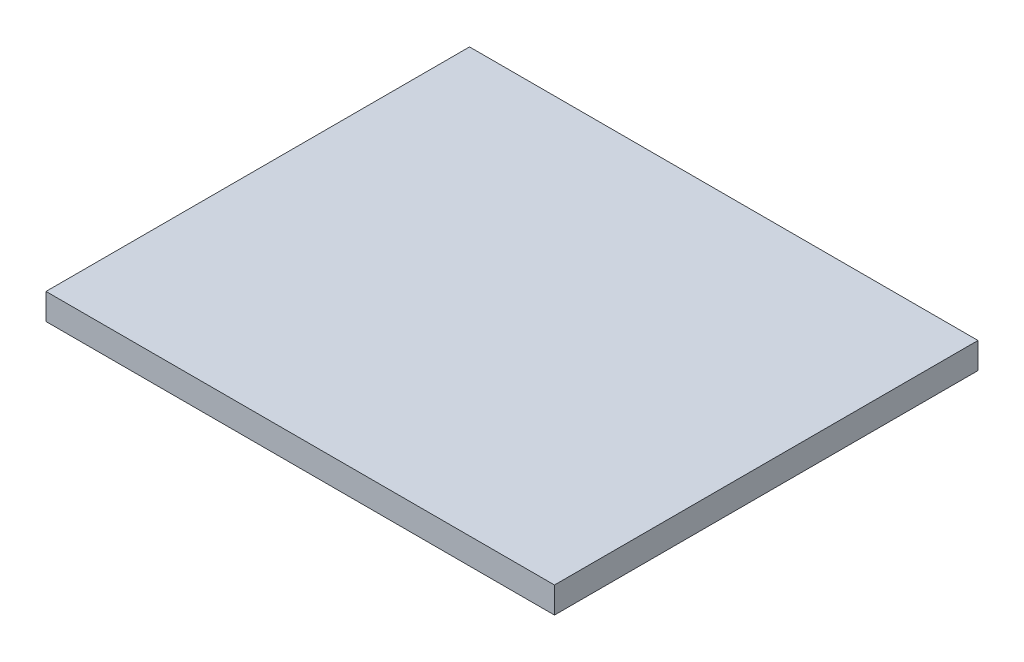
SolidWorks part; units mm, degrees
material "Ceramic Porcelain2"
ref_plane "Front Plane" through (0, 0, 0) normal (0, 0, 1) x (1, 0, 0)
ref_plane "Top Plane" through (0, 0, 0) normal (0, 1, 0) x (1, 0, 0)
ref_plane "Right Plane" through (0, 0, 0) normal (1, 0, 0) x (0, 0, -1)
sketch "Sketch1" plane through (0, 0, 0) normal (0, 1, 0) x (1, 0, 0)
  line L0 (0, 3.49) -> (4.19, 3.49)
  line L1 (0, 3.49) -> (-4.19, 3.49)
  line L2 (4.19, -3.49) -> (4.19, 3.49)
  line L3 (-4.19, -3.49) -> (-4.19, 3.49)
  line L4 (0, -3.49) -> (4.19, -3.49)
  line L5 (0, -3.49) -> (-4.19, -3.49)
  line L6 (2.625, 3.425) -> (2.625, 0.425)
  line L7 (-0.425, -3.425) -> (4.125, -3.425)
  line L8 (-0.425, 3.425) -> (2.625, 3.425)
  line L9 (-0.425, 3.425) -> (-0.425, -3.425)
  line L10 (2.625, 0.425) -> (4.125, 0.425)
  line L11 (4.125, 0.425) -> (4.125, -3.425)
  dimension "D1" = 0.065
  dimension "D2" = 3.765
extrude "Boss-Extrude1" add sketch "Sketch1" along normal blind 0.01 contours L6 L10 L11 L7 L9 L8
sketch "Sketch2" plane through (0, 0.01, 0) normal (0, 1, 0) x (1, 0, 0)
  line L18 (4.19, 3.49) -> (0, 3.49)
  line L19 (4.19, -3.49) -> (4.19, 3.49)
  line L20 (0, -3.49) -> (4.19, -3.49)
  line L21 (-4.19, -3.49) -> (0, -3.49)
  line L22 (-4.19, 3.49) -> (-4.19, -3.49)
  line L23 (0, 3.49) -> (-4.19, 3.49)
  line L24 (4.19, 3.49) -> (0, 3.49)
  line L25 (4.19, -3.49) -> (4.19, 3.49)
  line L26 (0, -3.49) -> (4.19, -3.49)
  line L27 (-4.19, -3.49) -> (0, -3.49)
  line L28 (-4.19, 3.49) -> (-4.19, -3.49)
  line L29 (0, 3.49) -> (-4.19, 3.49)
  dimension "D2" = 0
extrude "Boss-Extrude2" add sketch "Sketch2" along normal blind 0.43
